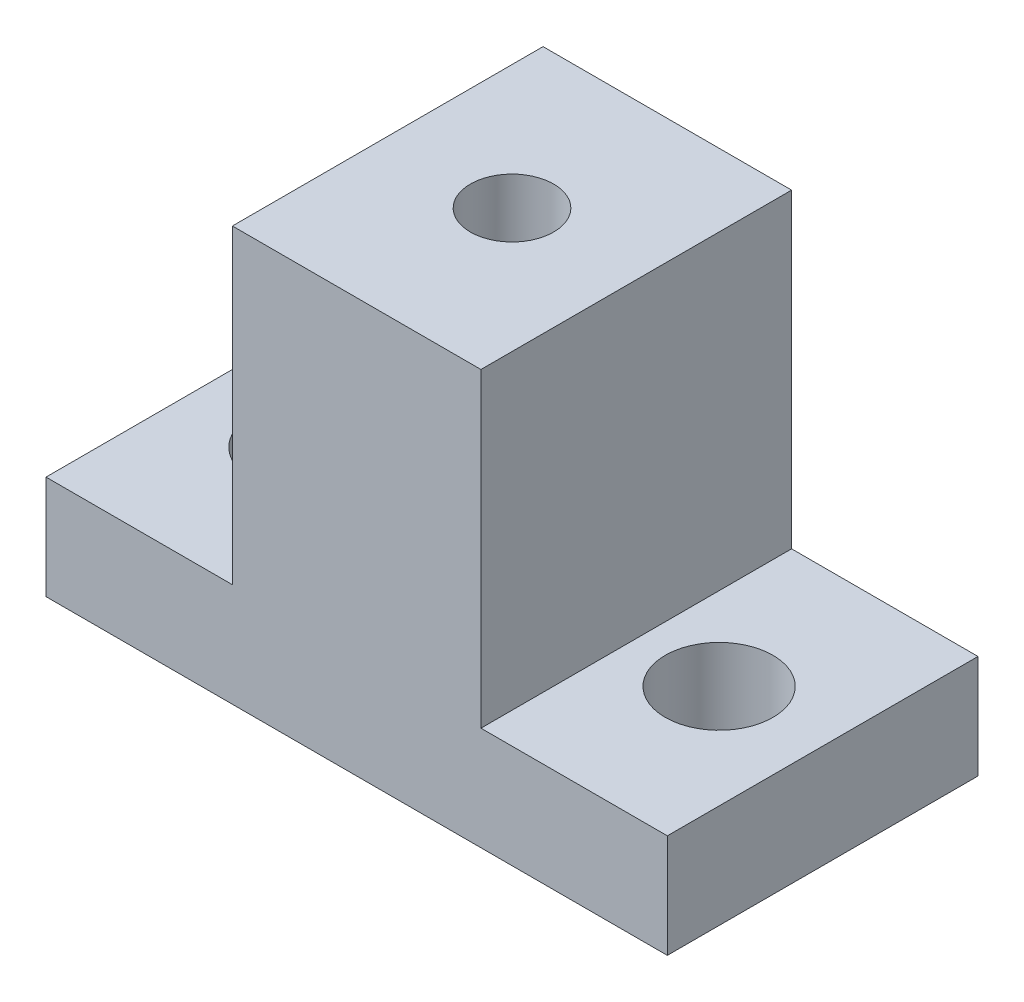
SolidWorks part; units mm, degrees
ref_plane "Front Plane" through (0, 0, 0) normal (0, 0, 1) x (1, 0, 0)
ref_plane "Top Plane" through (0, 0, 0) normal (0, 1, 0) x (1, 0, 0)
ref_plane "Right Plane" through (0, 0, 0) normal (1, 0, 0) x (0, 0, -1)
sketch "Sketch1" plane through (0, 0, 0) normal (0, 1, 0) x (1, 0, 0)
  line L1 (-19.05, 9.525) -> (19.05, 9.525)
  line L2 (-19.05, 9.525) -> (-19.05, -9.525)
  line L3 (-19.05, -9.525) -> (19.05, -9.525)
  line L4 (19.05, 9.525) -> (19.05, -9.525)
  dimension "D1" = 19.05
  dimension "D2" = 19.05
  dimension "D3" = 9.525
  dimension "D4" = 9.525
extrude "Boss-Extrude1" add sketch "Sketch1" along normal mid plane 25.4
sketch "Sketch2" plane through (0, 0, 9.525) normal (0, 0, 1) x (1, 0, 0)
  line L0 (-19.05, -12.7) -> (19.05, -12.7) construction
  line L1 (-19.05, 12.7) -> (-7.62, 12.7)
  line L2 (-19.05, 12.7) -> (-19.05, -6.35)
  line L3 (-19.05, -6.35) -> (-7.62, -6.35)
  line L4 (-7.62, 12.7) -> (-7.62, -6.35)
  dimension "D1" = 11.43
  dimension "D2" = 6.35
extrude "Cut-Extrude1" cut sketch "Sketch2" against normal through all
sketch "Sketch3" plane through (0, -6.35, 0) normal (0, 1, 0) x (1, 0, 0)
  circle A0 centre (-12.7, 0) radius 3.302
  dimension "D1" = 12.7
extrude "Cut-Extrude2" cut sketch "Sketch3" against normal through all
mirror "Mirror1" about plane through (0, 0, 0) normal (1, 0, 0) of "Cut-Extrude2", "Cut-Extrude1"
sketch "Sketch7" plane through (0, -12.7, 0) normal (0, -1, 0) x (1, 0, 0)
  circle A0 centre (0, 0) radius 6.35
extrude "Cut-Extrude6" cut sketch "Sketch7" against normal blind 19.05
hole_wizard "1/4-20 Tapped Hole2" positions "Sketch10" profile "Sketch9" tap size "1/4-20" standard "ANSI Inch" end condition through all
sketch "Sketch10" plane through (0, 12.7, 0) normal (0, 1, 0) x (1, 0, 0)
  point P0 (0, 0)
sketch "Sketch9" plane through (0, 12.7, 0) normal (1, 0, 0) x (0, 0, 1)
  line L0 (0, 0) -> (0, 25.4)
  line L1 (0, 25.4) -> (2.5527, 25.4)
  line L2 (2.5527, 25.4) -> (2.5527, 0)
  line L5 (2.5527, 0) -> (0, 0)
  line L11 (0, -6.35) -> (0, 107.95) construction
  dimension "Thru Tap Drill Dia." = 5.1054
  dimension "Thru Tap Drill Depth" = 25.4
cosmetic thread "Hole Thread2" parameters "D2"=6.35
